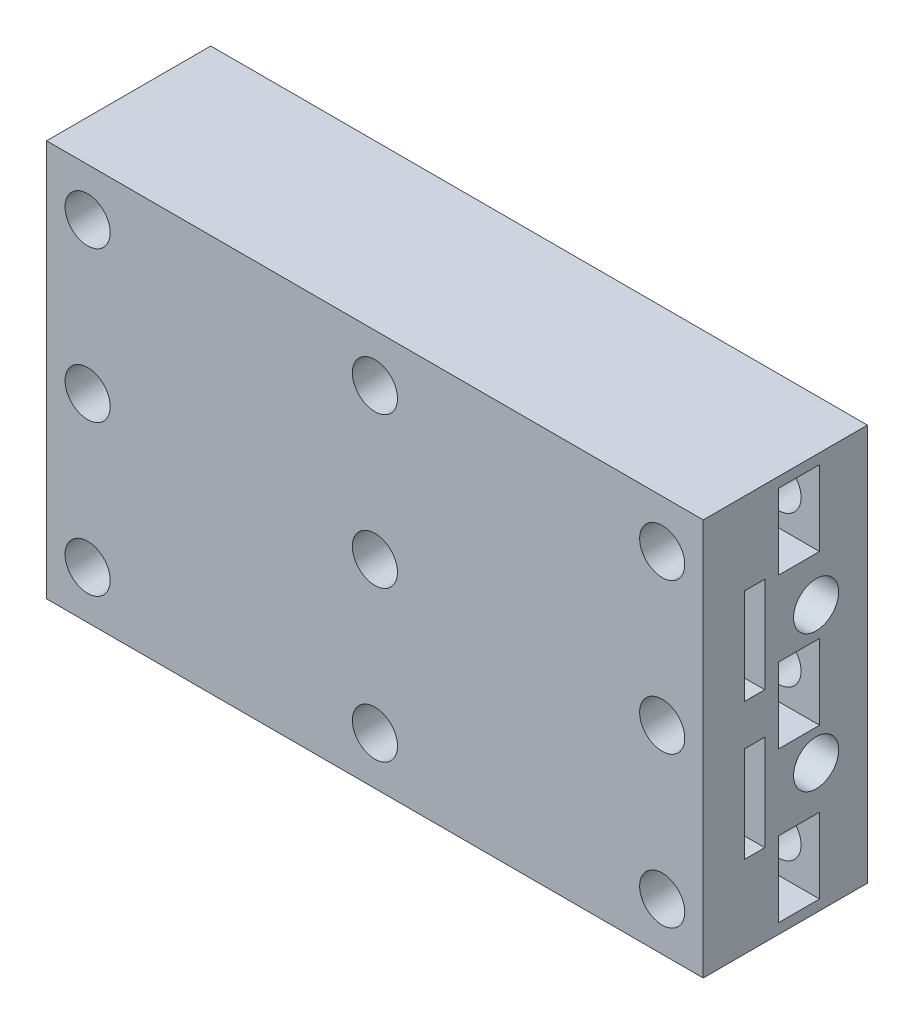
SolidWorks part; units mm, degrees
ref_plane "Plano frontal" through (0, 0, 0) normal (0, 0, 1) x (1, 0, 0)
ref_plane "Plano superior" through (0, 0, 0) normal (0, 1, 0) x (1, 0, 0)
ref_plane "Plano direito" through (0, 0, 0) normal (1, 0, 0) x (0, 0, -1)
sketch "Esboço1" plane through (0, 0, 0) normal (0, 0, 1) x (1, 0, 0)
  line L0 (-24, 0) -> (0, 0) construction
  line L1 (-24, 14.5) -> (24, 14.5)
  line L2 (-24, 14.5) -> (-24, -14.5)
  line L3 (-24, -14.5) -> (24, -14.5)
  line L4 (24, 14.5) -> (24, -14.5)
  line L5 (-24, 14.5) -> (24, -14.5) construction
  line L6 (-24, -14.5) -> (24, 14.5) construction
  line L7 (0, 0) -> (0, 14.5) construction
  circle A0 centre (-21, 11) radius 1.65
  circle A1 centre (-21, -11) radius 1.65
  circle A2 centre (21, -11) radius 1.65
  circle A3 centre (21, 11) radius 1.65
  point P0 (0, 0)
  dimension "D1" = 3.3
  dimension "D2" = 29
  dimension "D3" = 22
  dimension "D4" = 48
  dimension "D5" = 3
extrude "Ressalto-extrusão1" add sketch "Esboço1" along normal blind 12
sketch "Esboço2" plane through (0, 0, 0) normal (0, 1, 0) x (1, 0, 0)
  line L0 (-24, -9) -> (-8, -9)
  line L1 (-24, -12) -> (-24, 0) construction
  line L2 (24, 0) -> (-24, 0) construction
  line L3 (-18, 0) -> (-3.5, 0)
  line L4 (-18, 0) -> (-18, -7.5)
  line L5 (-18, -7.5) -> (-24, -7.5)
  line L6 (-24, -7.5) -> (-24, -9)
  line L8 (0, 0) -> (0, -12) construction
  line L9 (24, -12) -> (-24, -12) construction
  line L11 (24, -7.5) -> (24, -9)
  line L12 (18, -7.5) -> (24, -7.5)
  line L13 (18, 0) -> (18, -7.5)
  line L14 (24, -9) -> (8, -9)
  line L15 (3.5, -4.5) -> (3.5, 0)
  line L16 (-3.5, -4.5) -> (-3.5, 0)
  line L17 (3.5, 0) -> (18, 0)
  arc A0 (-8, -9) -> (-3.5, -4.5) centre (-8, -4.5) ccw
  arc A1 (8, -9) -> (3.5, -4.5) centre (8, -4.5) cw
  circle A2 centre (-23, 0) radius 0.6
  circle A3 centre (-21, 0) radius 0.6
  circle A4 centre (-19, 0) radius 0.6
  circle A5 centre (19, 0) radius 0.6
  circle A6 centre (21, 0) radius 0.6
  circle A7 centre (23, 0) radius 0.6
  dimension "D5" = 1.2
  dimension "D1" = 3
  dimension "D2" = 1.5
  dimension "D3" = 16
  dimension "D4" = 6
  dimension "D7" = 1
  dimension "D6" = 3
extrude "Corte-extrusão3" cut sketch "Esboço2" along normal blind 7 from offset 1.5
mirror "Espelhar1" about plane through (0, 0, 0) normal (0, 1, 0) of "Corte-extrusão3"
sketch "Esboço3" plane through (24, 0, 0) normal (1, 0, 0) x (0, 0, -1)
  line L0 (-7.5, -8.5) -> (-7.5, -1.5) construction
  line L1 (0, 0) -> (-12, 0) construction
  line L2 (-12, -14.5) -> (-12, 14.5) construction
  line L3 (-7.5, 5) -> (0, 5) construction
  line L4 (-7.5, 8.5) -> (-7.5, 1.5) construction
  line L5 (0, -14.5) -> (0, 14.5) construction
  circle A0 centre (-3.75, 5) radius 1.65
  circle A1 centre (-3.75, -5) radius 1.65
  point P7 (-7.5, -5)
  point P19 (-3.75, 5)
  dimension "D1" = 3.3
extrude "Corte-extrusão4" cut sketch "Esboço3" against normal blind 16
sketch "Esboço4" plane through (18, 0, 0) normal (-1, 0, 0) x (0, 0, 1)
  line L1 (6.9254, 5) -> (5.3377, 7.75)
  line L2 (5.3377, 7.75) -> (2.1623, 7.75)
  line L3 (2.1623, 7.75) -> (0.5746, 5)
  line L4 (0.5746, 5) -> (2.1623, 2.25)
  line L5 (2.1623, 2.25) -> (5.3377, 2.25)
  line L6 (5.3377, 2.25) -> (6.9254, 5)
  line L7 (6.9254, -5) -> (5.3377, -2.25)
  line L8 (5.3377, -2.25) -> (2.1623, -2.25)
  line L9 (2.1623, -2.25) -> (0.5746, -5)
  line L10 (0.5746, -5) -> (2.1623, -7.75)
  line L11 (2.1623, -7.75) -> (5.3377, -7.75)
  line L12 (5.3377, -7.75) -> (6.9254, -5)
  circle A0 centre (3.75, 5) radius 2.75 construction
  circle A1 centre (3.75, -5) radius 2.75 construction
  dimension "D1" = 5.5
extrude "Corte-extrusão5" cut sketch "Esboço4" against normal blind 2
sketch "Esboço5" plane through (24, 0, 0) normal (1, 0, 0) x (0, 0, -1)
  line L1 (-6.5, 2.75) -> (-3.5, 2.75)
  line L2 (-6.5, 2.75) -> (-6.5, -2.75)
  line L3 (-6.5, -2.75) -> (-3.5, -2.75)
  line L4 (-3.5, 2.75) -> (-3.5, -2.75)
  line L5 (-6.5, 2.75) -> (-3.5, -2.75) construction
  line L6 (-6.5, -2.75) -> (-3.5, 2.75) construction
  line L7 (-6.5, 8.25) -> (-3.5, 8.25)
  line L8 (-6.5, 8.25) -> (-6.5, 13.75)
  line L9 (-6.5, 13.75) -> (-3.5, 13.75)
  line L10 (-3.5, 8.25) -> (-3.5, 13.75)
  line L11 (-6.5, 8.25) -> (-3.5, 13.75) construction
  line L12 (-6.5, 13.75) -> (-3.5, 8.25) construction
  line L14 (-6.5, -8.25) -> (-3.5, -8.25)
  line L15 (-6.5, -8.25) -> (-6.5, -13.75)
  line L16 (-6.5, -13.75) -> (-3.5, -13.75)
  line L17 (-3.5, -8.25) -> (-3.5, -13.75)
  line L18 (-6.5, -8.25) -> (-3.5, -13.75) construction
  line L19 (-6.5, -13.75) -> (-3.5, -8.25) construction
  line L20 (0, 0) -> (-12, 0) construction
  line L21 (-12, -14.5) -> (-12, 14.5) construction
  point P0 (-5, 0)
  point P5 (-5, 11)
  point P12 (-5, -11)
  point P20 (-3.75, 5)
  dimension "D1" = 5.5
  dimension "D2" = 3
  dimension "D3" = 5
  dimension "D4" = 22
extrude "Corte-extrusão6" cut sketch "Esboço5" against normal blind 7
sketch "Esboço6" plane through (0, 0, 0) normal (0, 0, -1) x (-1, 0, 0)
  line L0 (0, 0) -> (0, -14.5) construction
  line L1 (24, -14.5) -> (-24, -14.5) construction
  line L2 (0, 0) -> (-9.4505, 0) construction
  circle A0 centre (-21, 0) radius 1.65
  circle A1 centre (21, 0) radius 1.65
  circle A2 centre (0, 0) radius 1.65
  circle A3 centre (0, 11) radius 1.65
  circle A4 centre (0, -11) radius 1.65
  point P3 (-21, 11)
  dimension "D1" = 3.3
extrude "Corte-extrusão7" cut sketch "Esboço6" against normal through all
mirror "Espelhar2" about plane through (0, 0, 0) normal (1, 0, 0) of "Corte-extrusão6", "Corte-extrusão5", "Corte-extrusão4"
sketch "Esboço7" plane through (0, 0, 0) normal (0, 0, -1) x (-1, 0, 0)
  circle A0 centre (0, 11) radius 3.4
  circle A1 centre (0, 0) radius 3.4
  circle A2 centre (0, -11) radius 3.4
  dimension "D1" = 6.8
extrude "Corte-extrusão9" cut sketch "Esboço7" against normal blind 3
